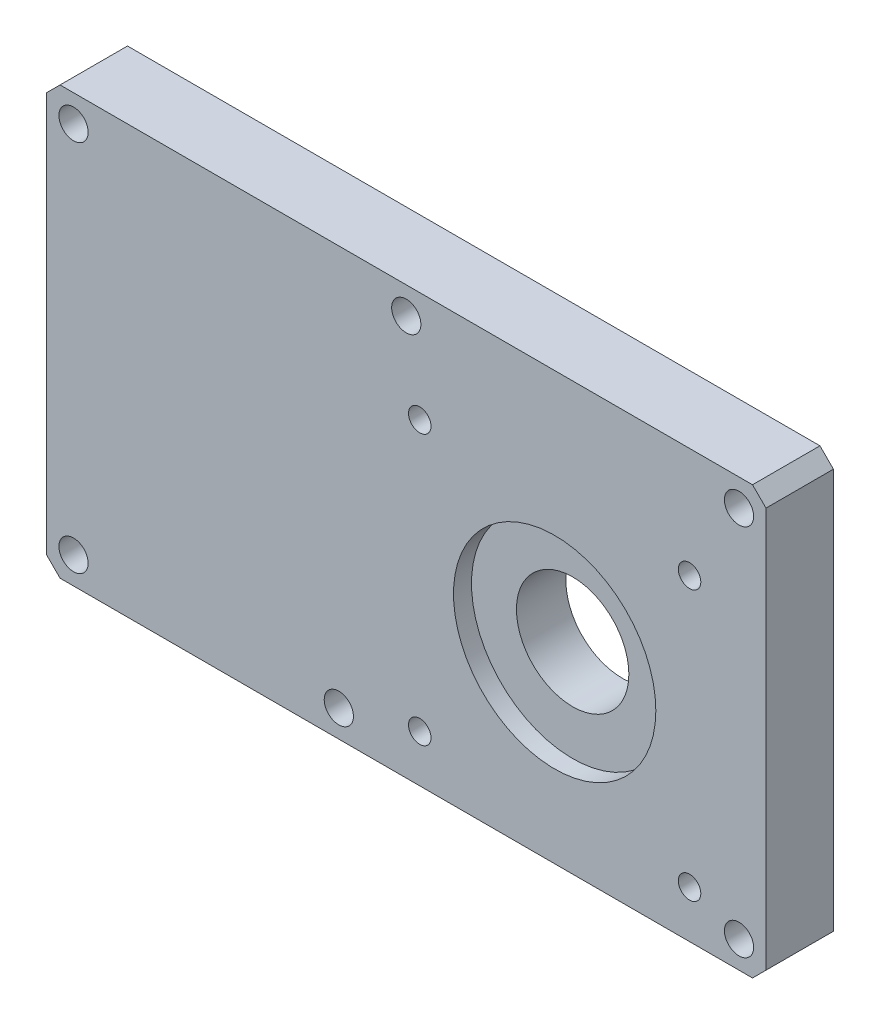
SolidWorks part; units mm, degrees
ref_plane "前视基准面" through (0, 0, 0) normal (0, 0, 1) x (1, 0, 0)
ref_plane "上视基准面" through (0, 0, 0) normal (0, 1, 0) x (1, 0, 0)
ref_plane "右视基准面" through (0, 0, 0) normal (1, 0, 0) x (0, 0, -1)
other "Configuration Table"
sketch "草图1" plane through (0, 0, 0) normal (0, 0, 1) x (1, 0, 0)
  line L1 (0, 0) -> (160, 0)
  line L2 (0, 0) -> (0, -95)
  line L3 (0, -95) -> (160, -95)
  line L4 (160, 0) -> (160, -95)
  dimension "D1" = 160
  dimension "D2" = 95
extrude "凸台-拉伸1" add sketch "草图1" along normal blind 15
chamfer "倒角1" distance 3 angle 45 4 edges at (160, -95, 7.5) (160, 0, 7.5) (0, -95, 7.5) (0, 0, 7.5)
sketch "草图2" plane through (0, 0, 0) normal (0, 0, -1) x (-1, 0, 0)
  circle A0 centre (-113, -54.25) radius 12.5
  dimension "D1" = 25
extrude "切除-拉伸1" cut sketch "草图2" against normal through all
hole_wizard "M6 螺纹孔1" positions "草图5" profile "草图4" tap size "M6" standard "GB"
sketch "草图5" plane through (0, 0, 0) normal (0, 0, -1) x (-1, 0, 0)
  point P0 (-143, -24.5)
  point P3 (-83, -24.5)
  point P6 (-83, -84.5)
  point P9 (-143, -84.5)
cosmetic thread "孔螺蚊线1" parameters "D1"=15, "D2"=6
cosmetic thread "孔螺蚊线2" parameters "D1"=15, "D2"=6
cosmetic thread "孔螺蚊线3" parameters "D1"=15, "D2"=6
cosmetic thread "孔螺蚊线4" parameters "D1"=15, "D2"=6
sketch "草图4" plane through (143, -24.5, 0) normal (1, 0, 0) x (0, 1, 0)
  line L0 (0, 0) -> (0, 21.5022)
  line L1 (0, 21.5022) -> (2.5, 20)
  line L2 (2.5, 20) -> (2.5, 0)
  line L5 (2.5, 0) -> (0, 0)
  line L10 (0, 21.5022) -> (-2.5, 20) construction
  line L11 (0, -6.35) -> (0, 107.95) construction
  dimension "螺纹孔钻头直径" = 5
  dimension "螺纹孔钻头深度" = 20
  dimension "导头角度" = 118
sketch "草图6" plane through (0, 0, 0) normal (0, 0, -1) x (-1, 0, 0)
  line L0 (-160, -92) -> (-160, -3) construction
  line L1 (-157, 0) -> (-3, 0) construction
  line L2 (-3, -95) -> (-157, -95) construction
  line L3 (0, -3) -> (0, -92) construction
  circle A0 centre (-154, -6) radius 5.25
  circle A1 centre (-80, -6) radius 5.25
  circle A2 centre (-6, -6) radius 5.25
  circle A4 centre (-6, -89) radius 5.25
  circle A5 centre (-154, -89) radius 5.25
  circle A6 centre (-65, -89) radius 5.25
  circle A7 centre (-80, -89) radius 5.25 [skipped]
  dimension "D1" = 10.5
  dimension "D6" = 10.5
  dimension "D2" = 6
  dimension "D3" = 6
  dimension "D7" = 6
  dimension "D8" = 65
  dimension "D4" = 3
  dimension "D5" = 2
extrude "切除-拉伸2" cut sketch "草图6" against normal blind 7
sketch "草图7" plane through (0, 0, 7) normal (0, 0, -1) x (-1, 0, 0)
  circle A0 centre (-154, -6) radius 5.25 construction
  circle A1 centre (-154, -6) radius 5.25 construction
  circle A2 centre (-154, -6) radius 3.25
  circle A3 centre (-80, -6) radius 3.25
  circle A4 centre (-6, -6) radius 3.25
  circle A6 centre (-6, -89) radius 3.25
  circle A7 centre (-154, -89) radius 3.25
  circle A8 centre (-65, -89) radius 3.25
  circle A9 centre (-65, -89) radius 5.25
  circle A10 centre (-65, -89) radius 5.25 construction
  circle A11 centre (-80, -89) radius 3.25 [skipped]
  dimension "D1" = 6.5
  dimension "D5" = 6.5
  dimension "D4" = 0
  dimension "D2" = 3
  dimension "D3" = 2
extrude "切除-拉伸3" cut sketch "草图7" against normal through all
sketch "草图8" plane through (0, 0, 15) normal (0, 0, 1) x (1, 0, 0)
  circle A0 centre (113, -54.25) radius 22.5
  dimension "D1" = 45
extrude "切除-拉伸4" cut sketch "草图8" against normal blind 4
